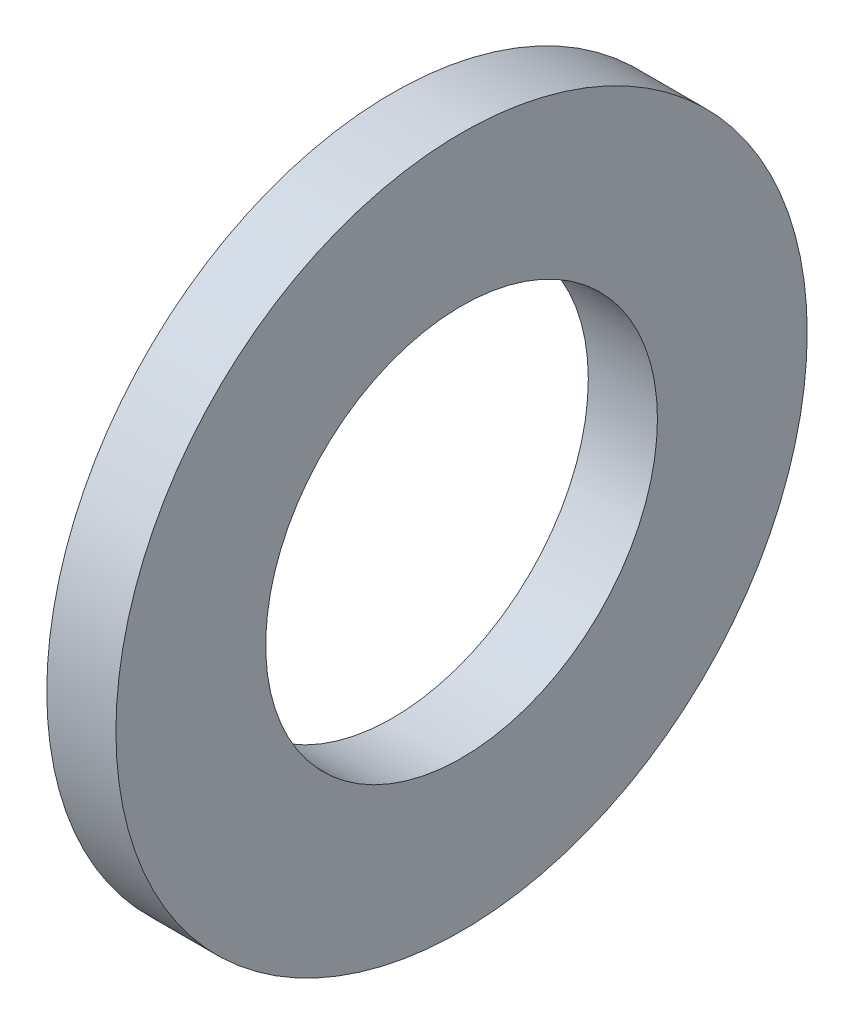
SolidWorks part; units mm, degrees
ref_plane "Front Plane" through (0, 0, 0) normal (0, 0, 1) x (1, 0, 0)
ref_plane "Top Plane" through (0, 0, 0) normal (0, 1, 0) x (1, 0, 0)
ref_plane "Right Plane" through (0, 0, 0) normal (1, 0, 0) x (0, 0, -1)
sketch "Sketch1" plane through (0, 0, 0) normal (1, 0, 0) x (0, 0, -1)
  circle A0 centre (0, 0) radius 15
  dimension "D1" = 30
extrude "Boss-Extrude1" add sketch "Sketch1" along normal blind 3
sketch "Sketch2" plane through (3, 0, 0) normal (1, 0, 0) x (0, 0, -1)
  circle A0 centre (0, 0) radius 8.5
  dimension "D1" = 17
extrude "Cut-Extrude1" cut sketch "Sketch2" against normal through all
